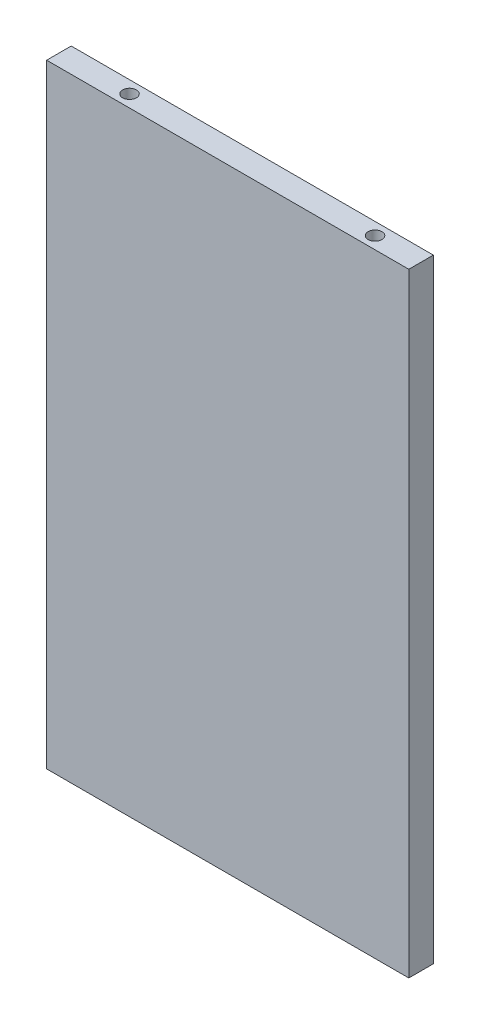
SolidWorks part; units mm, degrees
ref_plane "Front Plane" through (0, 0, 0) normal (0, 0, 1) x (1, 0, 0)
ref_plane "Top Plane" through (0, 0, 0) normal (0, 1, 0) x (1, 0, 0)
ref_plane "Right Plane" through (0, 0, 0) normal (1, 0, 0) x (0, 0, -1)
sketch "Sketch1" plane through (0, 0, 0) normal (0, 1, 0) x (1, 0, 0)
  line L1 (0, 0) -> (118, 0)
  line L2 (0, 0) -> (0, 8)
  line L3 (0, 8) -> (118, 8)
  line L4 (118, 0) -> (118, 8)
extrude "Extrude1" add sketch "Sketch1" along normal blind 200
sketch "Sketch2" plane through (0, 200, 0) normal (0, 1, 0) x (1, 0, 0)
  line L1 (118, 0) -> (118, 8) construction
  line L2 (0, 8) -> (0, 0) construction
  line L3 (0, 4) -> (23, 4) construction
  line L4 (23, 4) -> (103, 4) construction
  line L5 (103, 4) -> (118, 4) construction
hole_wizard "Ø4.5 (4.5) Diameter Hole1" positions "3DSketch1" profile "Sketch3" hole size "Ø4.5" standard "DIN"
sketch3d "3DSketch1"
  point P0 (23, 200, -4)
  point P3 (103, 200, -4)
sketch "Sketch3" plane through (23, 200, -4) normal (1, 0, 0) x (0, 0, 1)
  line L0 (0, 0) -> (0, 21.3519)
  line L1 (0, 21.3519) -> (2.25, 20)
  line L2 (2.25, 20) -> (2.25, 0)
  line L5 (2.25, 0) -> (0, 0)
  line L10 (0, 21.3519) -> (-2.25, 20) construction
  line L11 (0, -6.35) -> (0, 107.95) construction
  dimension "Hole Dia." = 4.5
  dimension "Hole Depth" = 20
  dimension "Drill Angle" = 118
sketch "Sketch4" plane through (0, 0, 0) normal (0, -1, 0) x (1, 0, 0)
  line L0 (0, -4) -> (23, -4) construction
  line L1 (0, -8) -> (0, 0) construction
  line L2 (23, -4) -> (103, -4) construction
  line L3 (103, -4) -> (118, -4) construction
  line L4 (118, 0) -> (118, -8) construction
hole_wizard "Ø4.5 (4.5) Diameter Hole2" positions "3DSketch2" profile "Sketch5" hole size "Ø4.5" standard "DIN"
sketch3d "3DSketch2"
  point P0 (23, 0, -4)
  point P3 (103, 0, -4)
sketch "Sketch5" plane through (23, 0, -4) normal (1, 0, 0) x (0, 0, -1)
  line L0 (0, 0) -> (0, 21.3519)
  line L1 (0, 21.3519) -> (2.25, 20)
  line L2 (2.25, 20) -> (2.25, 0)
  line L5 (2.25, 0) -> (0, 0)
  line L10 (0, 21.3519) -> (-2.25, 20) construction
  line L11 (0, -6.35) -> (0, 107.95) construction
  dimension "Hole Dia." = 4.5
  dimension "Hole Depth" = 20
  dimension "Drill Angle" = 118
